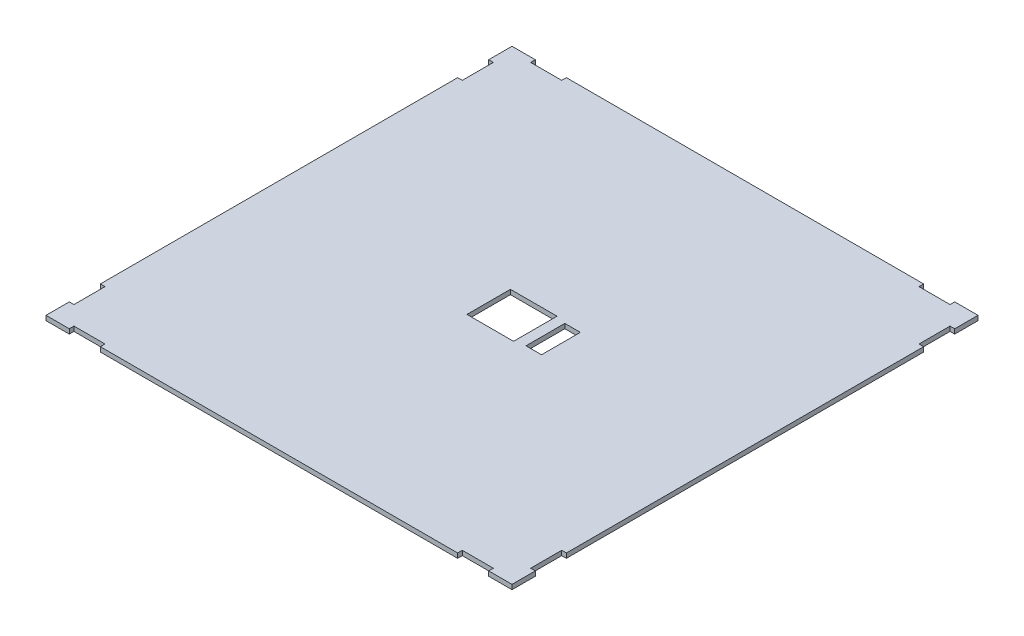
SolidWorks part; units mm, degrees
ref_plane "Alzado" through (0, 0, 0) normal (0, 0, 1) x (1, 0, 0)
ref_plane "Planta" through (0, 0, 0) normal (0, 1, 0) x (1, 0, 0)
ref_plane "Vista lateral" through (0, 0, 0) normal (1, 0, 0) x (0, 0, -1)
sketch "Croquis1" plane through (0, 0, 0) normal (0, 1, 0) x (1, 0, 0)
  line L0 (0, 0) -> (15, 0)
  line L1 (300, 0) -> (300, 15)
  line L2 (300, 300) -> (285, 300)
  line L3 (0, 300) -> (0, 285)
  line L4 (150, 0) -> (150, 136) construction
  line L5 (15, 0) -> (15, 3)
  line L6 (15, 3) -> (35, 3)
  line L7 (35, 3) -> (35, 0)
  line L8 (35, 0) -> (265, 0)
  line L9 (0, 0) -> (0, 15)
  line L10 (0, 15) -> (3, 15)
  line L11 (3, 15) -> (3, 35)
  line L12 (3, 35) -> (0, 35)
  line L13 (0, 150) -> (135, 150) construction
  line L14 (300, 0) -> (285, 0)
  line L15 (285, 0) -> (285, 3)
  line L16 (285, 3) -> (265, 3)
  line L17 (265, 3) -> (265, 0)
  line L18 (150, 150) -> (165, 150) construction
  line L19 (135, 136) -> (165, 136)
  line L20 (300, 15) -> (297, 15)
  line L21 (297, 15) -> (297, 35)
  line L22 (297, 35) -> (300, 35)
  line L23 (300, 300) -> (300, 285)
  line L24 (300, 35) -> (300, 265)
  line L25 (300, 285) -> (297, 285)
  line L26 (297, 285) -> (297, 265)
  line L27 (297, 265) -> (300, 265)
  line L28 (135, 136) -> (135, 164)
  line L29 (135, 164) -> (165, 164)
  line L30 (285, 300) -> (285, 297)
  line L31 (285, 297) -> (265, 297)
  line L32 (265, 297) -> (265, 300)
  line L33 (265, 300) -> (35, 300)
  line L34 (0, 300) -> (15, 300)
  line L35 (15, 300) -> (15, 297)
  line L36 (15, 297) -> (35, 297)
  line L37 (35, 297) -> (35, 300)
  line L38 (165, 136) -> (165, 164)
  line L39 (135, 150) -> (150, 150) construction
  line L40 (0, 285) -> (3, 285)
  line L41 (3, 285) -> (3, 265)
  line L42 (3, 265) -> (0, 265)
  line L43 (0, 265) -> (0, 35)
  line L44 (150, 164) -> (150, 150) construction
  line L45 (181.5, 150) -> (300, 150) construction
  line L46 (171.5, 137.5) -> (181.5, 137.5)
  line L47 (171.5, 137.5) -> (171.5, 162.5)
  line L48 (171.5, 162.5) -> (181.5, 162.5)
  line L49 (181.5, 137.5) -> (181.5, 162.5)
  line L50 (150, 150) -> (150, 136) construction
  line L52 (150, 164) -> (150, 300) construction
  point P41 (150, 150)
  point P56 (171.5, 150)
  dimension "D1" = 300
  dimension "D2" = 300
  dimension "D3" = 300
  dimension "D4" = 20
  dimension "D5" = 15
  dimension "D6" = 3
  dimension "D7" = 20
  dimension "D8" = 15
  dimension "D9" = 3
  dimension "D10" = 20
  dimension "D11" = 15
  dimension "D12" = 3
  dimension "D13" = 20
  dimension "D14" = 15
  dimension "D15" = 3
  dimension "D16" = 15
  dimension "D17" = 20
  dimension "D18" = 3
  dimension "D19" = 15
  dimension "D20" = 20
  dimension "D21" = 3
  dimension "D22" = 20
  dimension "D23" = 3
  dimension "D24" = 15
  dimension "D25" = 20
  dimension "D26" = 15
  dimension "D27" = 3
  dimension "D28" = 35
  dimension "D29" = 28
  dimension "D30" = 30
  dimension "D31" = 6.5
  dimension "D32" = 10
  dimension "D33" = 25
extrude "Saliente-Extruir2" add sketch "Croquis1" along normal blind 3
